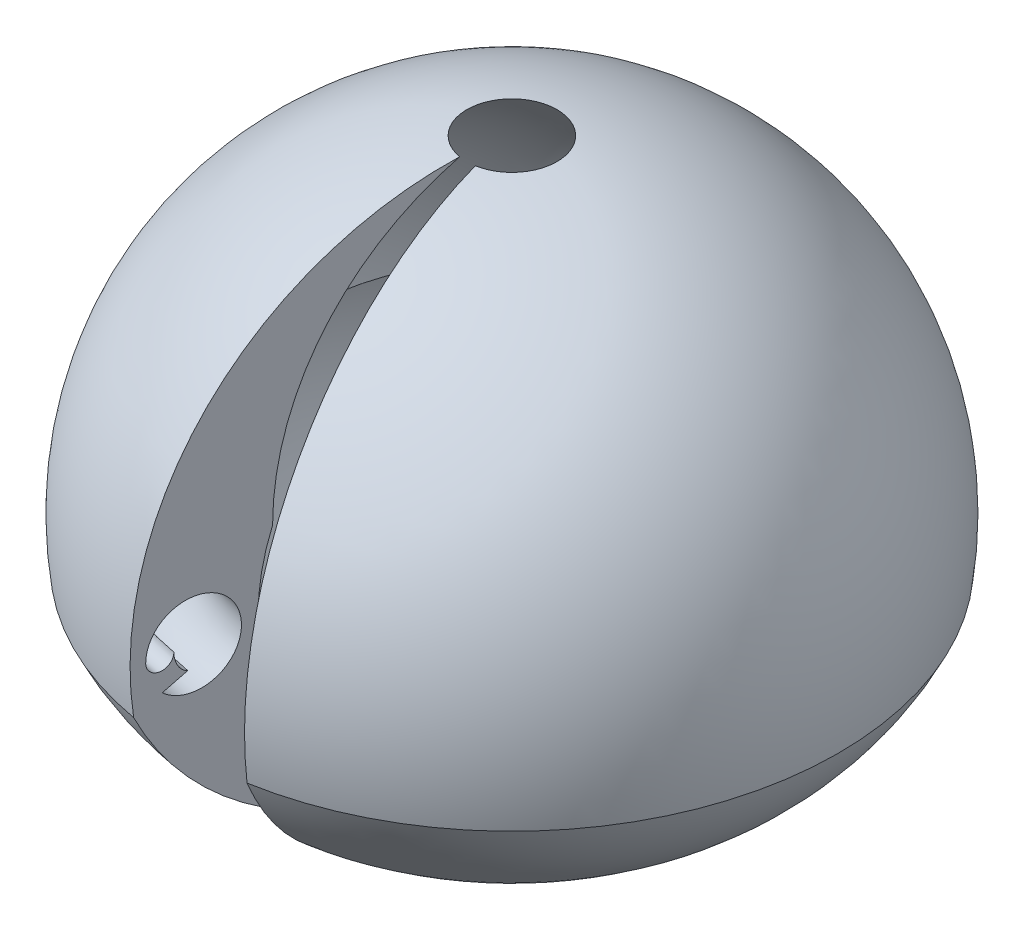
SolidWorks part; units mm, degrees
ref_plane "Front Plane" through (0, 0, 0) normal (0, 0, 1) x (1, 0, 0)
ref_plane "Top Plane" through (0, 0, 0) normal (0, 1, 0) x (1, 0, 0)
ref_plane "Right Plane" through (0, 0, 0) normal (1, 0, 0) x (0, 0, -1)
sketch "Sketch1" plane through (0, 0, 0) normal (1, 0, 0) x (0, 0, -1)
  line L0 (0, 0) -> (0, 2.751) construction
  line L1 (0, 0) -> (3.0399, 0) construction
  line L2 (0, 0) -> (-0.601, 0.601)
  line L3 (-0.601, 0.601) -> (0.371, 2.6855)
  line L4 (-0.601, 0.601) -> (1.699, 0.601)
  line L5 (0, 0) -> (0, -0.85)
  line L6 (0, 0) -> (0.601, 0.601)
  line L7 (0.601, 0.601) -> (2.6855, -0.371)
  line L8 (0.601, 0.601) -> (0.601, -1.699)
  line L9 (2.4, 0.15) -> (2.4, -0.02)
  line L10 (2.26, -0.02) -> (2.26, 0.16) construction
  line L11 (2.26, -0.02) -> (2.12, -0.02) construction
  line L12 (2.26, -0.02) -> (2.229, 0.1555) construction
  line L13 (2.26, -0.02) -> (2.5, -0.02) construction
  arc A0 (0.371, 2.6855) -> (2.6855, -0.371) centre (0, 0) cw
  arc A1 (0.371, 2.6855) -> (1.699, 0.601) centre (-0.601, 0.601) cw
  arc A2 (2.6855, -0.371) -> (0.601, -1.699) centre (0.601, 0.601) cw
  arc A3 (1.699, 0.601) -> (0.601, -1.699) centre (0, 0) cw
  arc A4 (2.4, -0.02) -> (2.6, -0.02) centre (2.5, -0.02) ccw
  arc A5 (2.6, -0.02) -> (2.5, -0.2608) centre (2.26, -0.02) ccw
  ellipse E0 centre (2.26, -0.02) end of major axis (2.26, 0.16) minor radius 0.14
  point P15 (1.8, 1.6)
  dimension "D13" = 0.34
  dimension "D1" = 0.85
  dimension "D2" = 2.3
  dimension "D3" = 45
  dimension "D4" = 110
  dimension "D5" = 10
  dimension "D6" = 45
  dimension "D7" = 70
  dimension "D8" = 65
  dimension "D9" = 0.14
  dimension "D10" = 0.18
  dimension "D11" = 0.17
  dimension "D12" = 0.24
  dimension "D14" = 1
  dimension "D15" = 0.85
  dimension "D16" = 2.4
revolve "Revolve1" add sketch "Sketch1" angle 170 about L0
